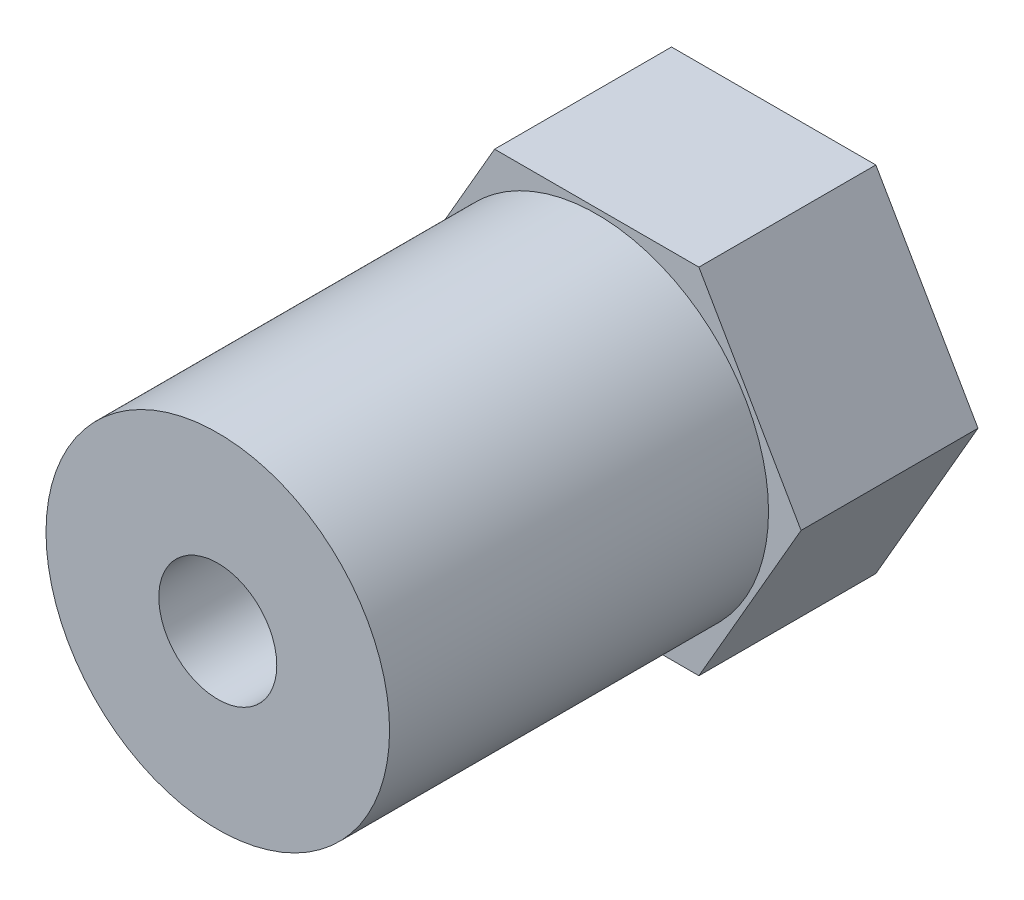
SolidWorks part; units mm, degrees
ref_plane "Front Plane" through (0, 0, 0) normal (0, 0, 1) x (1, 0, 0)
ref_plane "Top Plane" through (0, 0, 0) normal (0, 1, 0) x (1, 0, 0)
ref_plane "Right Plane" through (0, 0, 0) normal (1, 0, 0) x (0, 0, -1)
sketch "Sketch1" plane through (0, 0, 0) normal (0, 0, 1) x (1, 0, 0)
  line L1 (6.9282, 0) -> (3.4641, 6)
  line L2 (3.4641, 6) -> (-3.4641, 6)
  line L3 (-3.4641, 6) -> (-6.9282, 0)
  line L4 (-6.9282, 0) -> (-3.4641, -6)
  line L5 (-3.4641, -6) -> (3.4641, -6)
  line L6 (3.4641, -6) -> (6.9282, 0)
  circle A0 centre (0, 0) radius 6 construction
  circle A1 centre (0, 0) radius 1.625
  dimension "D1" = 12
  dimension "D2" = 3.25
extrude "Boss-Extrude1" add sketch "Sketch1" along normal blind 6
sketch "Sketch2" plane through (0, 0, 6) normal (0, 0, 1) x (1, 0, 0)
  circle A0 centre (0, 0) radius 5.825
  circle A1 centre (0, 0) radius 2
  dimension "D1" = 11.65
  dimension "D2" = 4
extrude "Boss-Extrude2" add sketch "Sketch2" along normal blind 12.85
